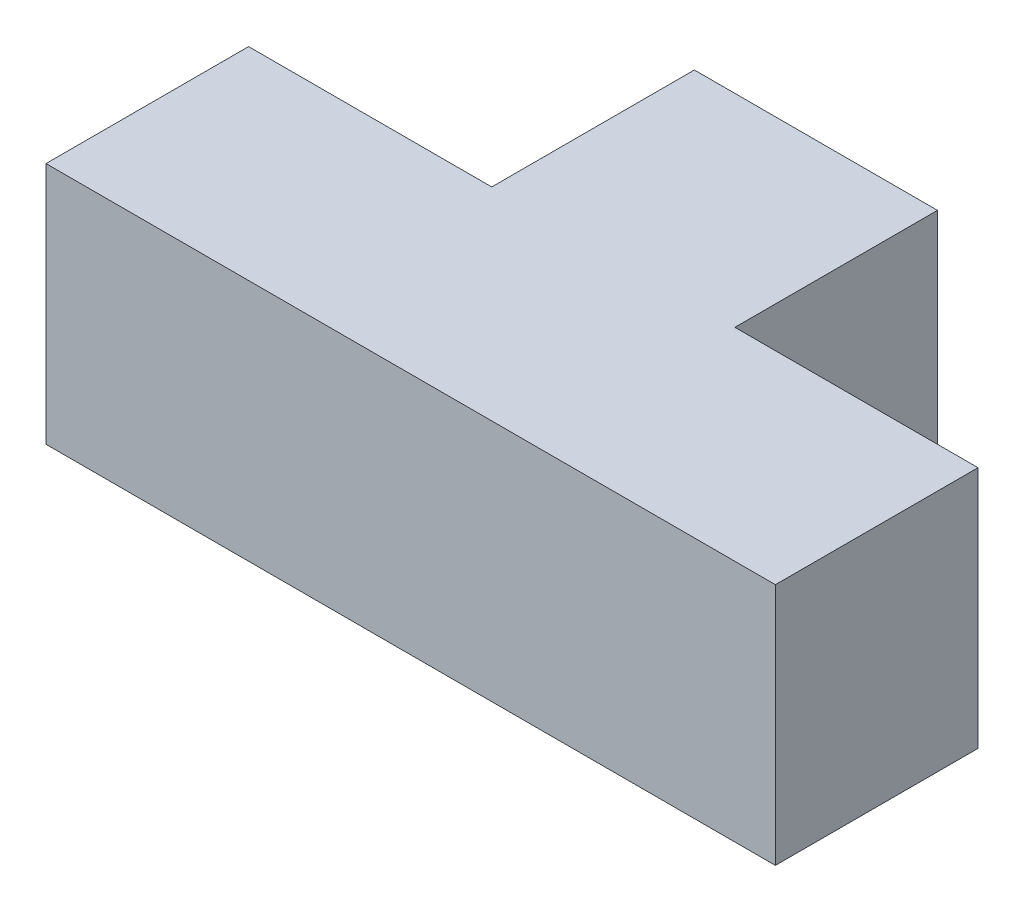
SolidWorks part; units mm, degrees
ref_plane "Front Plane" through (0, 0, 0) normal (0, 0, 1) x (1, 0, 0)
ref_plane "Top Plane" through (0, 0, 0) normal (0, 1, 0) x (1, 0, 0)
ref_plane "Right Plane" through (0, 0, 0) normal (1, 0, 0) x (0, 0, -1)
sketch "Sketch1" plane through (0, 0, 0) normal (0, 1, 0) x (1, 0, 0)
  line L0 (0, 0) -> (90, 0)
  line L1 (90, 0) -> (90, 25)
  line L2 (90, 25) -> (60, 25)
  line L3 (60, 25) -> (60, 50)
  line L4 (60, 50) -> (30, 50)
  line L5 (30, 50) -> (30, 25)
  line L6 (30, 25) -> (0, 25)
  line L7 (0, 25) -> (0, 0)
  dimension "D1" = 90
  dimension "D2" = 25
extrude "Boss-Extrude1" add sketch "Sketch1" along normal blind 30
